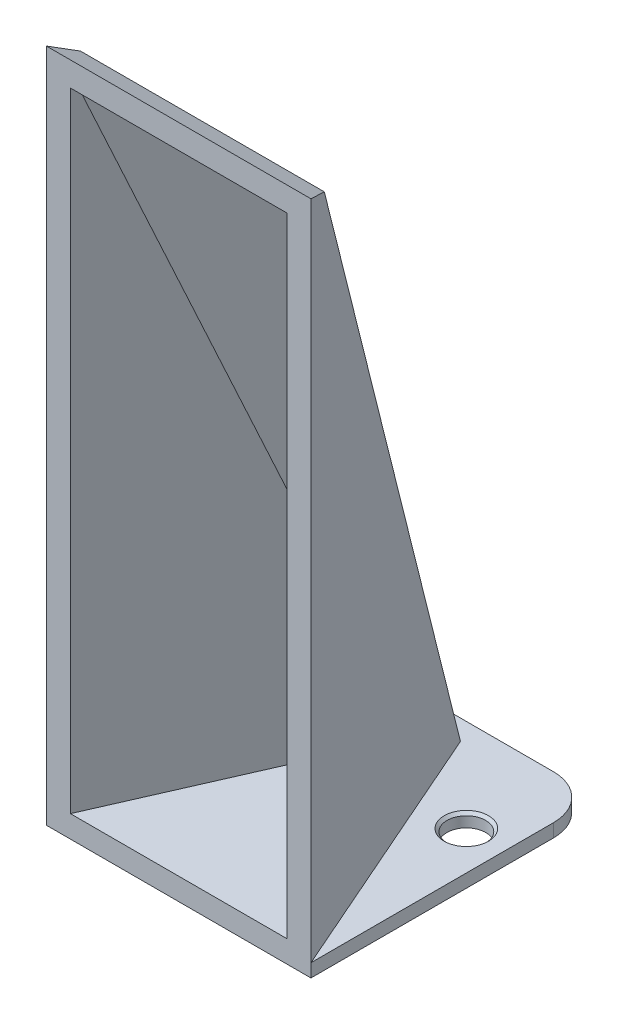
SolidWorks part; units mm, degrees
ref_plane "Front Plane" through (0, 0, 0) normal (0, 0, 1) x (1, 0, 0)
ref_plane "Top Plane" through (0, 0, 0) normal (0, 1, 0) x (1, 0, 0)
ref_plane "Right Plane" through (0, 0, 0) normal (1, 0, 0) x (0, 0, -1)
sketch "Sketch1" plane through (0, 0, 0) normal (0, 1, 0) x (1, 0, 0)
  line L1 (0, 0) -> (60, 0)
  line L2 (0, 0) -> (0, 65)
  line L3 (0, 65) -> (60, 65)
  line L4 (60, 0) -> (60, 65)
  dimension "D1" = 60
  dimension "D2" = 65
extrude "Boss-Extrude2" add sketch "Sketch1" along normal blind 3
sketch "Sketch3" plane through (0, 3, 0) normal (0, 1, 0) x (1, 0, 0)
  line L0 (0, 0) -> (60, 0)
  line L1 (60, 0) -> (33.5, 60.3929)
  line L2 (33.5, 60.3929) -> (26.5, 60.3929)
  line L3 (26.5, 60.3929) -> (0, 0)
  line L4 (30, -1000) -> (30, 49000) construction
  point P9 (30, 0)
  dimension "D1" = 3.5
  dimension "D2" = 7
extrude "Boss-Extrude4" add sketch "Sketch3" along normal blind 150
sketch "Sketch5" plane through (0, 0, 0) normal (-1, 0, 0) x (0, 0, 1)
  line L0 (-60.3929, 3) -> (-5.3918, 150.4899)
  line L1 (-5.3918, 150.4899) -> (0, 153)
  line L2 (0, 153) -> (0, 157.7325)
  line L3 (0, 157.7325) -> (-60.3929, 157.7325)
  line L4 (-60.3929, 157.7325) -> (-60.3929, 3)
extrude "Cut-Extrude2" cut sketch "Sketch5" against normal blind 150
fillet "Fillet1" radius 10 2 edges at (60, 1.5, -65) (0, 1.5, -65)
shell "Shell1" thickness 5
hole_wizard "M10x1.25 Tapped Hole1" positions "Sketch6" profile "Sketch7" tap size "M10x1.25" standard "ANSI Metric" end condition through all
sketch "Sketch6" plane through (0, 3, 0) normal (0, 1, 0) x (1, 0, 0)
  line L0 (60, 0) -> (60, 55) construction
  line L1 (0, 55) -> (0, 0) construction
  point P0 (51.25, 43.9809)
  point P2 (8.75, 43.9809)
  dimension "D1" = 8.75
  dimension "D2" = 8.75
sketch "Sketch7" plane through (51.25, 3, -43.9809) normal (1, 0, 0) x (0, 0, 1)
  line L0 (0, 0) -> (0, 3)
  line L1 (0, 3) -> (4.4, 3)
  line L2 (4.4, 3) -> (4.4, 0.625)
  line L3 (4.4, 0.625) -> (5.025, 0)
  line L5 (5.025, 0) -> (0, 0)
  line L6 (-4.4, 0.625) -> (-5.025, 0) construction
  line L11 (0, -6.35) -> (0, 107.95) construction
  dimension "Thru Tap Drill Dia." = 8.8
  dimension "Thru Tap Drill Depth" = 3
  dimension "Near C'Sink Dia." = 10.05
  dimension "Near C'Sink Angle" = 90
cosmetic thread "Hole Thread1" parameters "D2"=10
cosmetic thread "Hole Thread2" parameters "D2"=10
